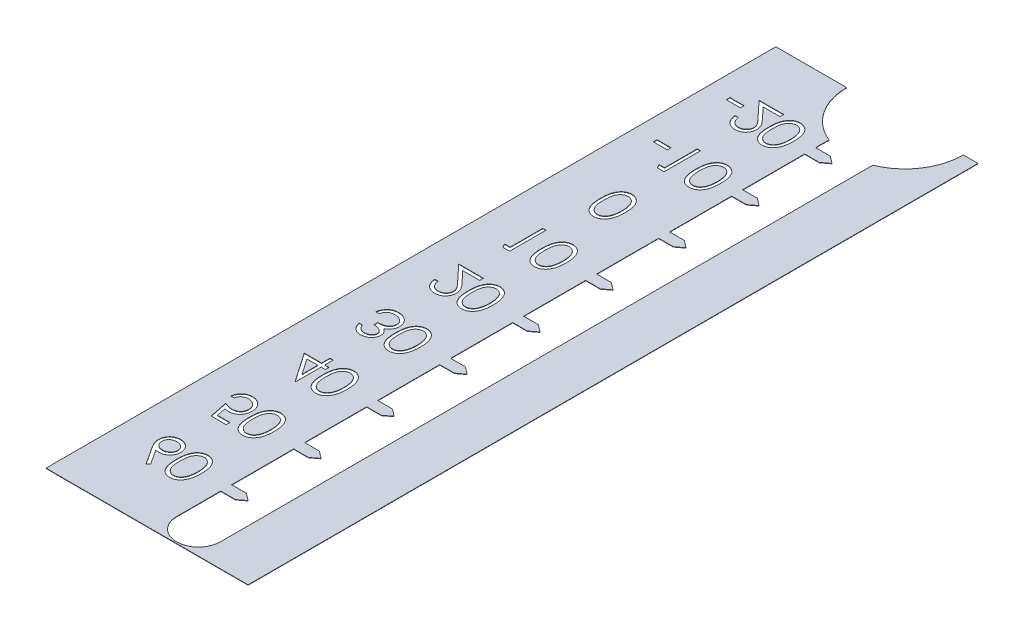
SolidWorks part; units mm, degrees
ref_plane "Front Plane" through (0, 0, 0) normal (0, 0, 1) x (1, 0, 0)
ref_plane "Top Plane" through (0, 0, 0) normal (0, 1, 0) x (1, 0, 0)
ref_plane "Right Plane" through (0, 0, 0) normal (1, 0, 0) x (0, 0, -1)
sketch "Sketch1" plane through (0, 0, 0) normal (0, 1, 0) x (1, 0, 0)
  line L1 (0, 0) -> (40, 0)
  line L2 (0, 0) -> (0, -100)
  line L3 (0, -100) -> (40, -100)
  line L4 (40, 0) -> (40, -100)
  dimension "D1" = 100
  dimension "D2" = 40
extrude "Boss-Extrude1" add sketch "Sketch1" along normal blind 0.05
sketch "Sketch3" plane through (0, 0, 0) normal (0, -1, 0) x (1, 0, 0)
  line L0 (48.332, 0) -> (-9.6396, 0) construction
  line L1 (48.332, 10) -> (-9.6396, 10) construction
  line L2 (48.332, 20) -> (-9.6396, 20) construction
  line L3 (48.332, 30) -> (-9.6396, 30) construction
  line L4 (48.332, 40) -> (-9.6396, 40) construction
  line L5 (48.332, 50) -> (-9.6396, 50) construction
  line L6 (48.332, 60) -> (-9.6396, 60) construction
  line L7 (48.332, 70) -> (-9.6396, 70) construction
  line L8 (48.332, 80) -> (-9.6396, 80) construction
  line L9 (48.332, 90) -> (-9.6396, 90) construction
  line L10 (48.332, 100) -> (-9.6396, 100) construction
  line L11 (40, 0) -> (40, 10) construction
  line L12 (40, 10) -> (40, 20) construction
  line L13 (40, 20) -> (40, 30) construction
  line L14 (40, 30) -> (40, 40) construction
  line L15 (40, 40) -> (40, 50) construction
  line L16 (40, 50) -> (40, 60) construction
  line L17 (40, 60) -> (40, 70) construction
  line L18 (40, 70) -> (40, 80) construction
  line L19 (40, 80) -> (40, 90) construction
  line L20 (40, 90) -> (40, 100) construction
  line L21 (0, 7.5) -> (40, 7.5) construction
  line L22 (0, 0) -> (0, 100) construction
  line L23 (0, 17.5) -> (40, 17.5) construction
  line L24 (0, 27.5) -> (40, 27.5) construction
  line L25 (0, 37.5) -> (40, 37.5) construction
  line L26 (0, 47.5) -> (40, 47.5) construction
  line L27 (0, 57.5) -> (40, 57.5) construction
  line L28 (0, 67.5) -> (40, 67.5) construction
  line L29 (0, 77.5) -> (40, 77.5) construction
  line L30 (0, 87.5) -> (40, 87.5) construction
  line L31 (0, 97.5) -> (40, 97.5) construction
  line L32 (30, -6.863) -> (30, 104.3463) construction
  line L33 (27, 96.8) -> (27, 90.75)
  line L34 (33, 96.8) -> (33, 7.4162)
  line L35 (27, 9.25) -> (29.0106, 9.25)
  line L36 (29.0106, 20.75) -> (27, 20.75)
  line L37 (29.0106, 10.75) -> (27, 10.75)
  line L38 (29.0106, 10.75) -> (30, 10)
  line L39 (30, 10) -> (29.0106, 9.25)
  line L40 (29.0106, 20.75) -> (30, 20)
  line L41 (30, 20) -> (29.0106, 19.25)
  line L42 (27, 19.25) -> (29.0106, 19.25)
  line L43 (29.0106, 30.75) -> (27, 30.75)
  line L44 (29.0106, 30.75) -> (30, 30)
  line L45 (30, 30) -> (29.0106, 29.25)
  line L46 (27, 29.25) -> (29.0106, 29.25)
  line L47 (29.0106, 40.75) -> (27, 40.75)
  line L48 (29.0106, 40.75) -> (30, 40)
  line L49 (30, 40) -> (29.0106, 39.25)
  line L50 (27, 39.25) -> (29.0106, 39.25)
  line L51 (29.0106, 50.75) -> (27, 50.75)
  line L52 (29.0106, 50.75) -> (30, 50)
  line L53 (30, 50) -> (29.0106, 49.25)
  line L54 (27, 49.25) -> (29.0106, 49.25)
  line L55 (29.0106, 60.75) -> (27, 60.75)
  line L56 (29.0106, 60.75) -> (30, 60)
  line L57 (30, 60) -> (29.0106, 59.25)
  line L58 (27, 59.25) -> (29.0106, 59.25)
  line L59 (29.0106, 70.75) -> (27, 70.75)
  line L60 (29.0106, 70.75) -> (30, 70)
  line L61 (30, 70) -> (29.0106, 69.25)
  line L62 (27, 69.25) -> (29.0106, 69.25)
  line L63 (29.0106, 80.75) -> (27, 80.75)
  line L64 (29.0106, 80.75) -> (30, 80)
  line L65 (30, 80) -> (29.0106, 79.25)
  line L66 (27, 79.25) -> (29.0106, 79.25)
  line L67 (29.0106, 90.75) -> (27, 90.75)
  line L68 (29.0106, 90.75) -> (30, 90)
  line L69 (30, 90) -> (29.0106, 89.25)
  line L70 (27, 89.25) -> (29.0106, 89.25)
  line L71 (27, 9.25) -> (27, 7.4162)
  line L72 (27, 19.25) -> (27, 10.75)
  line L73 (27, 29.25) -> (27, 20.75)
  line L74 (27, 39.25) -> (27, 30.75)
  line L75 (27, 49.25) -> (27, 40.75)
  line L76 (27, 59.25) -> (27, 50.75)
  line L77 (27, 69.25) -> (27, 60.75)
  line L78 (27, 79.25) -> (27, 70.75)
  line L79 (27, 89.25) -> (27, 80.75)
  arc A0 (27, 7.4162) -> (33, 7.4162) centre (30, 0) ccw
  arc A1 (33, 96.8) -> (27, 96.8) centre (30, 96.8) ccw
  text T0 "-20" font "Century Gothic" height 5
  text T1 "-10" font "Century Gothic" height 5
  text T2 "0" font "Century Gothic" height 5
  text T3 "10" font "Century Gothic" height 5
  text T4 "20" font "Century Gothic" height 5
  text T5 "30" font "Century Gothic" height 5
  text T6 "40" font "Century Gothic" height 5
  text T7 "50" font "Century Gothic" height 5
  text T8 "60" font "Century Gothic" height 5
  dimension "D8" = 16
  dimension "D9" = 6
  dimension "D1" = 11
  dimension "D2" = 2.5
  dimension "D3" = 10
  dimension "D4" = 40
  dimension "D6" = 10
  dimension "D7" = 30
  dimension "D10" = 3.2
  dimension "D11" = 0.75
  dimension "D12" = 0.75
  dimension "D13" = 9
  dimension "D14" = 10
  dimension "D5" = 10
extrude "Cut-Extrude3" cut sketch "Sketch3" against normal through all
sketch "Sketch4" plane through (0, 0, 0) normal (0, -1, 0) x (1, 0, 0)
  line L0 (40, 100) -> (40, 0) construction
  line L1 (-5.2313, 103.2706) -> (12.3077, 103.2706)
  line L2 (-5.2313, 103.2706) -> (-5.2313, -6.6519)
  line L3 (-5.2313, -6.6519) -> (12.3077, -6.6519)
  line L4 (12.3077, 103.2706) -> (12.3077, -6.6519)
  dimension "D1" = 27.6923
extrude "Cut-Extrude4" cut sketch "Sketch4" against normal through all both and the other way through all
